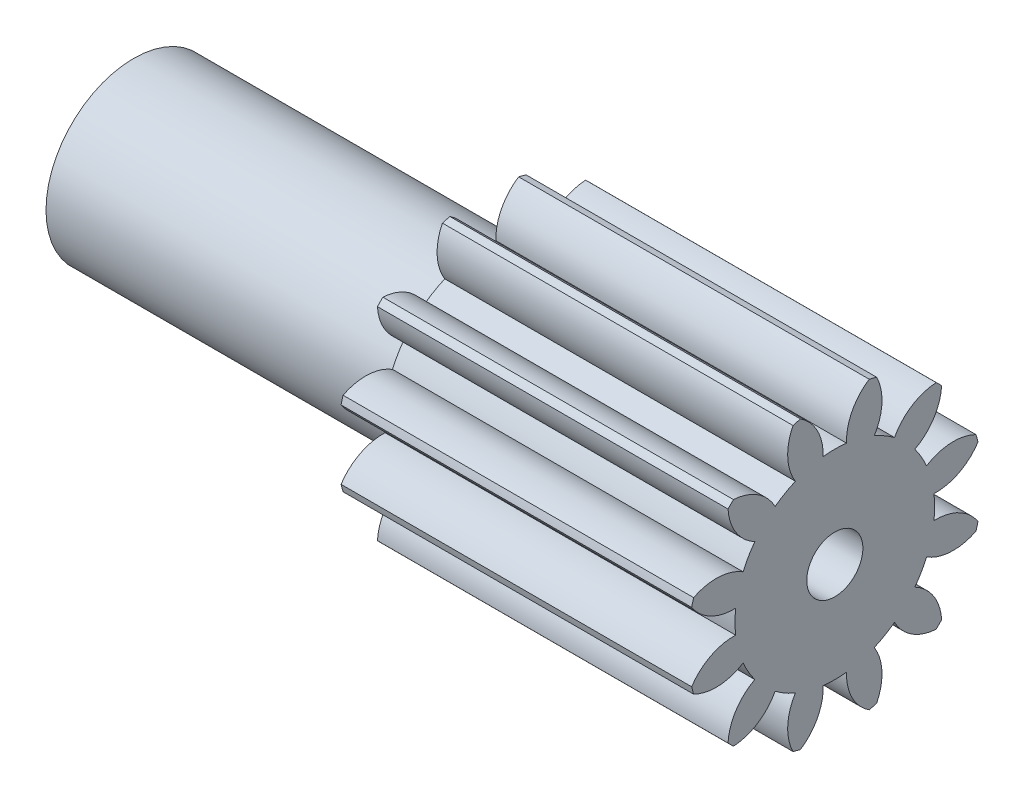
SolidWorks part; units mm, degrees
ref_plane "Plane1" through (0, 0, 0) normal (0, 0, 1) x (1, 0, 0)
ref_plane "Plane2" through (0, 0, 0) normal (0, 1, 0) x (1, 0, 0)
ref_plane "Plane3" through (0, 0, 0) normal (1, 0, 0) x (0, 0, -1)
sketch "HoldingSke" plane through (0, 0, 0) normal (0, 1, 0) x (1, 0, 0)
  line L0 (0, 0) -> (3.2605, -0.693)
  line L1 (-15, 0) -> (100, 0) construction
  line L2 (0, 0) -> (-2.1039, 2.3779)
  line L3 (0, 0) -> (-11.863, 4.5341)
  line L4 (0, 0) -> (8.4473, 1.7955)
  line L5 (0, 0) -> (-9.3695, -3.4946)
  line L6 (0, 0) -> (-4.1448, -2.7965)
  line L7 (-2.1039, 2.3779) -> (0.0486, 12.1435)
  line L8 (-76.2, 54.61) -> (-76.1, 54.61)
  line L9 (-71.009, 38.7566) -> (-53.1078, 45.2721)
  line L10 (-76.2, 71.12) -> (104.1128, 71.12)
  line L11 (0, 0) -> (-5, 0)
  line L12 (-76.2, 101.6) -> (-76.19, 101.6)
  line L13 (24.9733, 27.94) -> (52.9518, 28.4284)
  line L14 (24.9733, 27.94) -> (24.9743, 27.94)
  line L15 (24.9733, 27.94) -> (100.4006, 29.5858)
  line L16 (-63.627, -0.3) -> (-12.827, -0.3)
  circle A0 centre (0, 0) radius 0.4
  circle A1 centre (0, 0) radius 1.25
  circle A2 centre (0, 0) radius 1.25
  circle A3 centre (0, 0) radius 0.4
  dimension "MHD" = 2.5
  dimension "Hub_dia" = 2.5
  dimension "Bore" = 0.8
  dimension "MBD" = 0.8
  dimension "Num_teeth" = 12
  dimension "Pitch" = 3.3333
  dimension "Overall_len" = 10
  dimension "Show_teeth" = 12
  dimension "Thickness" = 5
  dimension "OAL" = 10.0001
  dimension "T_dim" = 0.1
  dimension "Ap" = 20
  dimension "H" = 19.05
  dimension "Pitch_radius" = 180.3128
  dimension "Width" = 5
  dimension "Backlash" = 0.01
  dimension "Addendum_fac" = 1
  dimension "Dedendum_fac" = 1.25
  dimension "Clearance_fac" = 0.25
  dimension "Dedendum_add" = 0.001
  dimension "Module" = 0.3
sketch "BasProSke" plane through (0, 0, 0) normal (0, 1, 0) x (1, 0, 0)
  line L0 (-10, 0) -> (60, 0) construction
  line L1 (0, 0) -> (0, 2.1)
  line L2 (0, 0) -> (5, 0)
  line L3 (5, 0) -> (5, 2.1)
  line L4 (5, 2.1) -> (0, 2.1)
  dimension "Thickness" = 5
  dimension "Diameter" = 4.2
revolve "Base-Revolve" add sketch "BasProSke" angle 360 about L0
sketch "TooCutSke" plane through (0, 0, 0) normal (1, 0, 0) x (0, 0, -1)
  line L1 (0, 0) -> (0, 107) construction
  line L2 (0, 0) -> (-0.2524, 1.7822) construction
  line L3 (0, 0) -> (-0.9249, 3.4519) construction
  line L4 (-0.2524, 1.7822) -> (-0.4625, 1.7259) construction
  arc A0 (0.1667, 1.4142) -> (-0.1667, 1.4142) centre (0, 0) ccw
  arc A1 (0.5203, 2.0607) -> (-0.5203, 2.0607) centre (0, 0) ccw
  circle A2 centre (0, 0) radius 1.8 construction
  circle A3 centre (0, 0) radius 1.6914 construction
  arc A4 (-0.1667, 1.4142) -> (-0.5203, 2.0607) centre (-0.8863, 1.4407) ccw
  arc A5 (0.5203, 2.0607) -> (0.1667, 1.4142) centre (0.8863, 1.4407) ccw
  dimension "Root_dia" = 2.848
  dimension "Overcut_dia" = 4.2508
  dimension "Pitch_dia" = 3.6
  dimension "Base_dia" = 3.3829
  dimension "Flank_rad" = 0.72
  dimension "Half_ang" = 15
  dimension "Half_CT" = 0.2174
extrude "ToothCut" cut sketch "TooCutSke" along normal through all
fillet "Breaks" [suppressed] radius 0.006
fillet "RootFillets" [suppressed] radius 0.076
pattern_circular "TeethCuts" count 12 every 30 about axis through (-10, 0, 0) along (1, 0, 0) of "ToothCut", "RootFillets", "Breaks"
sketch "HubNeaOneSke" plane through (0, 0, 0) normal (-1, 0, 0) x (0, 0, 1)
  circle A0 centre (0, 0) radius 1.25
  dimension "Diameter" = 2.5
extrude "HubNearOne" add sketch "HubNeaOneSke" along normal blind 5.0001
sketch "HubNeaBotSke" plane through (0, 0, 0) normal (-1, 0, 0) x (0, 0, 1)
  circle A0 centre (0, 0) radius 1.25
  dimension "Diameter" = 2.5
extrude "HubNearBoth" [suppressed] add sketch "HubNeaBotSke" along normal blind 2.5
ref_plane "FarPln" through (5, 0, 0) normal (1, 0, 0) x (0, 0, -1)
sketch "HubFarSke" plane through (5, 0, 0) normal (1, 0, 0) x (0, 0, -1)
  circle A0 centre (0, 0) radius 1.25
  dimension "Diameter" = 2.5
extrude "HubFar" [suppressed] add sketch "HubFarSke" along normal blind 2.5
sketch "BorSke" plane through (0, 0, 0) normal (1, 0, 0) x (0, 0, -1)
  circle A0 centre (0, 0) radius 0.4
  dimension "Diameter" = 0.8
extrude "Bore" cut sketch "BorSke" along normal mid plane 20.0001
sketch "KeySke" plane through (0, 0, 0) normal (1, 0, 0) x (0, 0, -1)
  line L0 (-0.05, 0) -> (-0.05, 0.5)
  line L1 (-0.05, 0.5) -> (0.05, 0.5)
  line L2 (0.05, 0.5) -> (0.05, 0)
  line L3 (0, 0) -> (0, 34) construction
  line L4 (-0.05, 0) -> (0.05, 0)
  dimension "Offset" = 0.5
  dimension "Width" = 0.1
extrude "Keyway" [suppressed] cut sketch "KeySke" along normal mid plane 20.0001
pattern_circular "Keyway2" [suppressed] count 2 every 90 about axis through (-10, 0, 0) along (1, 0, 0)
equation "' \"Module@HoldingSke\" = 6.35"
equation "' \"Num_teeth@HoldingSke\" = 12"
equation "' \"Ap@HoldingSke\" =  20"
equation "' \"Ap@HoldingSke\" = 20"
equation "' \"Width@HoldingSke\" = 0.5 * 25.4"
equation "' \"Hub_dia@HoldingSke\"= 1 * 25.4"
equation "' \"Hub_dia@HoldingSke\" = 1 * 25.4"
equation "' \"Overall_len@HoldingSke\" = 1.0 * 25.4"
equation "' \"Bore@HoldingSke\" = 0.75 * 25.4"
equation "' \"T_dim@HoldingSke\" = 0.1 * 25.4"
equation "' \"Width@KeySke\" = 0.25 * 25.4"
equation "' \"Show_teeth@HoldingSke\" = 13"
equation "' \"Backlash@HoldingSke\" = 0.009 * 25.4"
equation "' \"Addendum_fac@HoldingSke\" = 1.0"
equation "' \"Dedendum_fac@HoldingSke\" = 1.25"
equation "' \"Dedendum_add@HoldingSke\" = 0.00005 * 25.4"
equation "' \"Clearance_fac@HoldingSke\" = 0.25"
equation "\"Pitch@HoldingSke\" = 1 / \"Module@HoldingSke\""
equation "\"Overcut_dia@TooCutSke\" = (\"Num_teeth@HoldingSke\" + 2 * \"Addendum_fac@HoldingSke\") / \"Pitch@HoldingSke\" + 0.002 * 25.4"
equation "\"Pitch_dia@TooCutSke\" = \"Num_teeth@HoldingSke\" / \"Pitch@HoldingSke\""
equation "\"Base_dia@TooCutSke\" = \"Num_teeth@HoldingSke\" / \"Pitch@HoldingSke\" * cos((\"Ap@HoldingSke\"  * 3.14159265 / 180))"
equation "\"Root_dia@TooCutSke\" = (\"Num_teeth@HoldingSke\" + 2) / \"Pitch@HoldingSke\" - 2 * (\"Addendum_fac@HoldingSke\" + \"Dedendum_fac@HoldingSke\") / \"Pitch@HoldingSke\" - \"Dedendum_add@HoldingSke\" * 2"
equation "\"Half_ang@TooCutSke\" = 180 / \"Num_teeth@HoldingSke\""
equation "\"Half_CT@TooCutSke\" = \"Num_teeth@HoldingSke\" / \"Pitch@HoldingSke\" * sin((3.14159265 / 2 / \"Num_teeth@HoldingSke\")) / 2 - 7 * \"Backlash@HoldingSke\" / 4"
equation "\"Flank_rad@TooCutSke\" = \"Num_teeth@HoldingSke\" / \"Pitch@HoldingSke\" / 5"
equation "\"Radius@RootFillets\" = \"Clearance_fac@HoldingSke\" / \"Pitch@HoldingSke\" + \"Dedendum_add@HoldingSke\""
equation "\"Break_rad@Breaks\" = 0.02 / \"Pitch@HoldingSke\""
equation "\"Thickness@HoldingSke\" = \"Width@HoldingSke\""
equation "\"OAL@HoldingSke\" = \"Thickness@HoldingSke\""
equation "\"MHD@HoldingSke\" = (\"Num_teeth@HoldingSke\" + 2) / \"Pitch@HoldingSke\" - 2 * (\"Addendum_fac@HoldingSke\" + \"Dedendum_fac@HoldingSke\")  / \"Pitch@HoldingSke\" - \"Dedendum_add@HoldingSke\" * 2"
equation "\"MBD@HoldingSke\" = (\"Num_teeth@HoldingSke\" + 2) / \"Pitch@HoldingSke\" - 2 * (\"Addendum_fac@HoldingSke\" + \"Dedendum_fac@HoldingSke\")  / \"Pitch@HoldingSke\" - \"Dedendum_add@HoldingSke\" * 2 - 0.002 * 25.4"
equation "\"MHD@HoldingSke\" = ((sgn( \"MHD@HoldingSke\" - \"Hub_dia@HoldingSke\" )-1)*( \"MHD@HoldingSke\" - \"Hub_dia@HoldingSke\" ))/-2+ \"Hub_dia@HoldingSke\""
equation "\"MBD@HoldingSke\" = ((sgn( \"MBD@HoldingSke\" - \"Bore@HoldingSke\" )-1)*( \"MBD@HoldingSke\" - \"Bore@HoldingSke\" ))/-2+ \"Bore@HoldingSke\""
equation "\"OAL@HoldingSke\" = ((sgn( \"OAL@HoldingSke\" - \"Overall_len@HoldingSke\" )+1)*( \"OAL@HoldingSke\" - \"Overall_len@HoldingSke\" ))/2 + \"Overall_len@HoldingSke\" + 0.000002 * 25.4"
equation "\"Num_teeth@TeethCuts\" = int( \"Show_teeth@HoldingSke\" ) + 1"
equation "\"Num_teeth@TeethCuts\" = ((sgn( \"Num_teeth@TeethCuts\" - \"Num_teeth@HoldingSke\" )-1)*( \"Num_teeth@TeethCuts\" - \"Num_teeth@HoldingSke\" ))/-2+ \"Num_teeth@HoldingSke\""
equation "\"Num_teeth@TeethCuts\" = ((sgn( \"Num_teeth@TeethCuts\" - 2.0)+1)*( \"Num_teeth@TeethCuts\" - 2.0))/2 +2.0"
equation "\"Angle@TeethCuts\" = 360.0 / \"Num_teeth@HoldingSke\""
equation "\"Diameter@BasProSke\" = (\"Num_teeth@HoldingSke\" + 2 * \"Addendum_fac@HoldingSke\") / \"Pitch@HoldingSke\""
equation "\"Thickness@BasProSke\"  = \"Thickness@HoldingSke\""
equation "' \"Fillet_rad@BasProSke\" =  \"Thickness@HoldingSke\" * 0.05"
equation "' \"Fillet_rad@BasProSke\" = \"Thickness@HoldingSke\" * 0.05"
equation "\"MHD@HoldingSke\" = ((sgn( \"MHD@HoldingSke\" - \"Root_dia@TooCutSke\" )-1)*( \"MHD@HoldingSke\" - \"Root_dia@TooCutSke\" ))/-2+ \"Root_dia@TooCutSke\""
equation "\"Diameter@HubNeaOneSke\" = \"MHD@HoldingSke\""
equation "\"Length@HubNearOne\" = \"OAL@HoldingSke\" - \"Thickness@BasProSke\""
equation "\"Diameter@HubNeaBotSke\" = \"MHD@HoldingSke\""
equation "\"Length@HubNearBoth\" = ( \"OAL@HoldingSke\" - \"Thickness@BasProSke\" ) / 2.0"
equation "\"Thickness@FarPln\" = \"Thickness@BasProSke\""
equation "\"Diameter@HubFarSke\" = \"MHD@HoldingSke\""
equation "\"Length@HubFar\" = ( \"OAL@HoldingSke\" - \"Thickness@BasProSke\" ) / 2.0"
equation "\"Diameter@BorSke\" = \"MBD@HoldingSke\""
equation "\"D1@Bore\" = \"OAL@HoldingSke\" * 2.0"
equation "\"D1@Keyway\" = \"OAL@HoldingSke\" * 2.0"
equation "\"Offset@KeySke\" = \"T_dim@HoldingSke\" + \"MBD@HoldingSke\" / 2.0"
